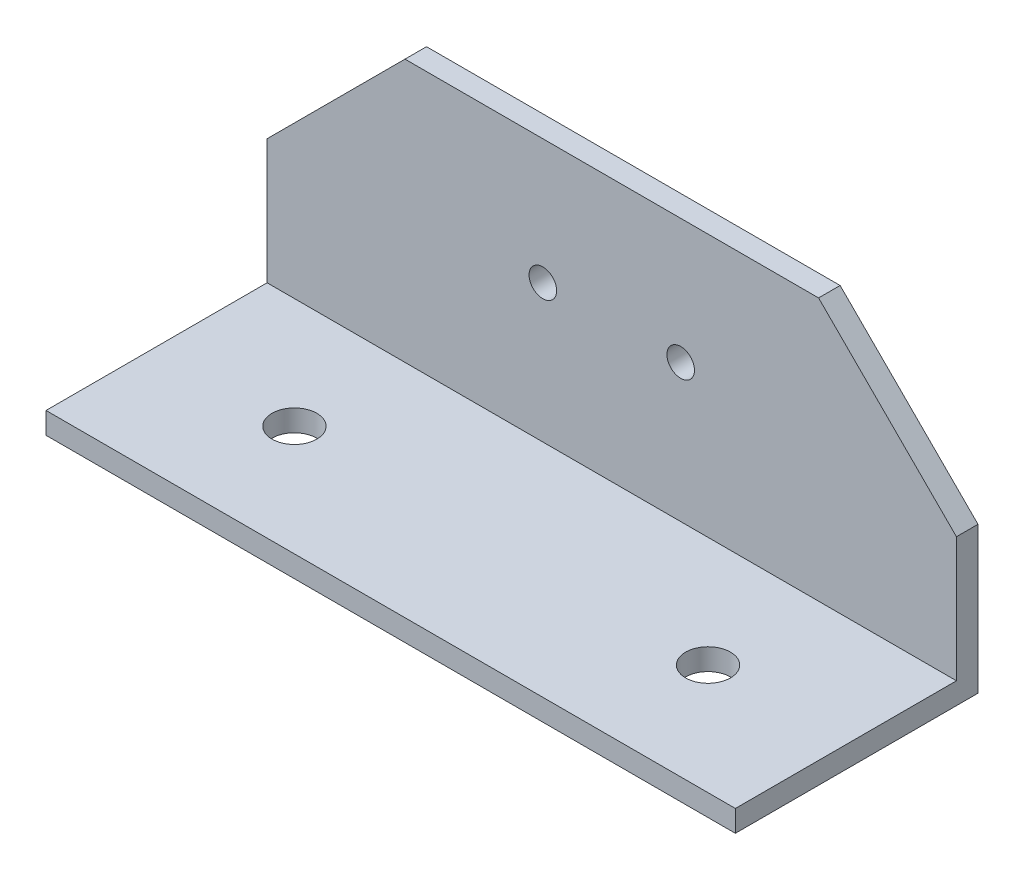
SolidWorks part; units mm, degrees
ref_plane "Front Plane" through (0, 0, 0) normal (0, 0, 1) x (1, 0, 0)
ref_plane "Top Plane" through (0, 0, 0) normal (0, 1, 0) x (1, 0, 0)
ref_plane "Right Plane" through (0, 0, 0) normal (1, 0, 0) x (0, 0, -1)
sketch "Sketch1" plane through (0, 0, 0) normal (1, 0, 0) x (0, 0, -1)
  line L0 (0, 0) -> (32.073, 0)
  line L1 (32.073, 0) -> (32.073, 38.1)
extrude "Extrude-Thin1" add sketch "Sketch1" along normal blind 100 thin
sketch "Sketch2" plane through (0, 0, -35.198) normal (0, 0, -1) x (-1, 0, 0)
  line L0 (-50, 38.1) -> (-50, -3.125) construction
  line L1 (-100, 38.1) -> (0, 38.1) construction
  line L2 (-100, -3.125) -> (0, -3.125) construction
  line L3 (-101.0395, 20) -> (-1.0395, 20) construction
  line L4 (-100, -3.125) -> (-100, 38.1) construction
  circle A0 centre (-40, 20) radius 2
  circle A1 centre (-60, 20) radius 2
  dimension "D2" = 40
  dimension "D1" = 23.125
extrude "Cut-Extrude1" cut sketch "Sketch2" against normal through all
chamfer "Chamfer1" distance 20 angle 45 2 edges at (100, 38.1, -33.6355) (0, 38.1, -33.6355)
sketch "Sketch3" plane through (0, 0, 0) normal (0, 1, 0) x (-1, 0, 0)
  line L0 (-100, -16.0365) -> (0, -16.0365) construction
  line L1 (-100, 0) -> (-100, -32.073) construction
  line L2 (0, 0) -> (0, -32.073) construction
  line L4 (-100, 0) -> (0, 0) construction
  line L5 (-50, 0) -> (-50, -35.198) construction
  line L6 (-80, -35.198) -> (-20, -35.198) construction
  circle A0 centre (-80, -16.0365) radius 3.25
  circle A1 centre (-20, -16.0365) radius 3.25
  dimension "D1" = 20
extrude "Cut-Extrude2" cut sketch "Sketch3" against normal through all
